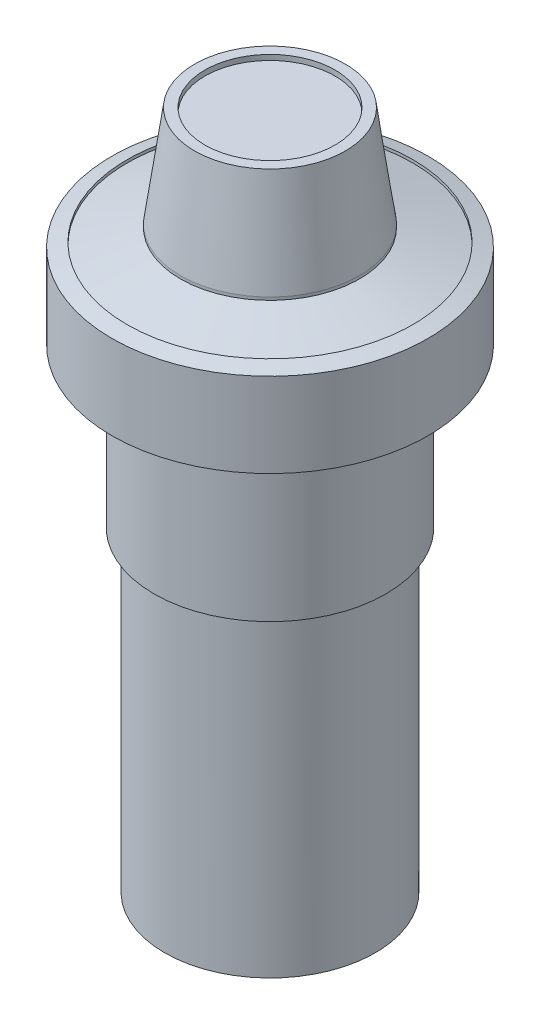
SolidWorks part; units mm, degrees
ref_plane "Front Plane" through (0, 0, 0) normal (0, 0, 1) x (1, 0, 0)
ref_plane "Top Plane" through (0, 0, 0) normal (0, 1, 0) x (1, 0, 0)
ref_plane "Right Plane" through (0, 0, 0) normal (1, 0, 0) x (0, 0, -1)
sketch "Sketch1" plane through (0, 0, 0) normal (0, 1, 0) x (1, 0, 0)
  circle A0 centre (0, 0) radius 11
  dimension "D1" = 22
extrude "Boss-Extrude1" add sketch "Sketch1" along normal blind 15
sketch "Sketch2" plane through (0, 15, 0) normal (0, 1, 0) x (1, 0, 0)
  circle A0 centre (0, 0) radius 15
  dimension "D1" = 30
extrude "Boss-Extrude2" add sketch "Sketch2" along normal blind 8
sketch "Sketch3" plane through (0, 0, 0) normal (0, 0, 1) x (1, 0, 0)
  line L0 (0, 31.3692) -> (0, -6.0032) construction
  line L1 (-13.5657, 23.4226) -> (-15, 23)
  line L2 (-8.4962, 24.9164) -> (-7.1518, 34.488)
  line L3 (-7.1518, 34.488) -> (0, 34.488)
  line L4 (0, 34.488) -> (0, 23)
  line L5 (0, 23) -> (-15, 23)
  line L6 (-13.5657, 23.4226) -> (-13.5657, 23.1451)
  line L7 (-13.5657, 23.1451) -> (-8.4962, 24.6389)
  line L8 (-8.4962, 24.6389) -> (-8.4962, 24.9164)
revolve "Revolve1" add sketch "Sketch3" angle 360 about L0
sketch "Sketch4" plane through (0, 34.488, 0) normal (0, 1, 0) x (1, 0, 0)
  circle A0 centre (0, 0) radius 6.1771
extrude "Cut-Extrude1" cut sketch "Sketch4" against normal blind 0.5
sketch "Sketch5" plane through (0, 0, 0) normal (0, -1, 0) x (1, 0, 0)
  circle A0 centre (0, 0) radius 10
  dimension "D1" = 20
extrude "Boss-Extrude3" add sketch "Sketch5" along normal blind 30
